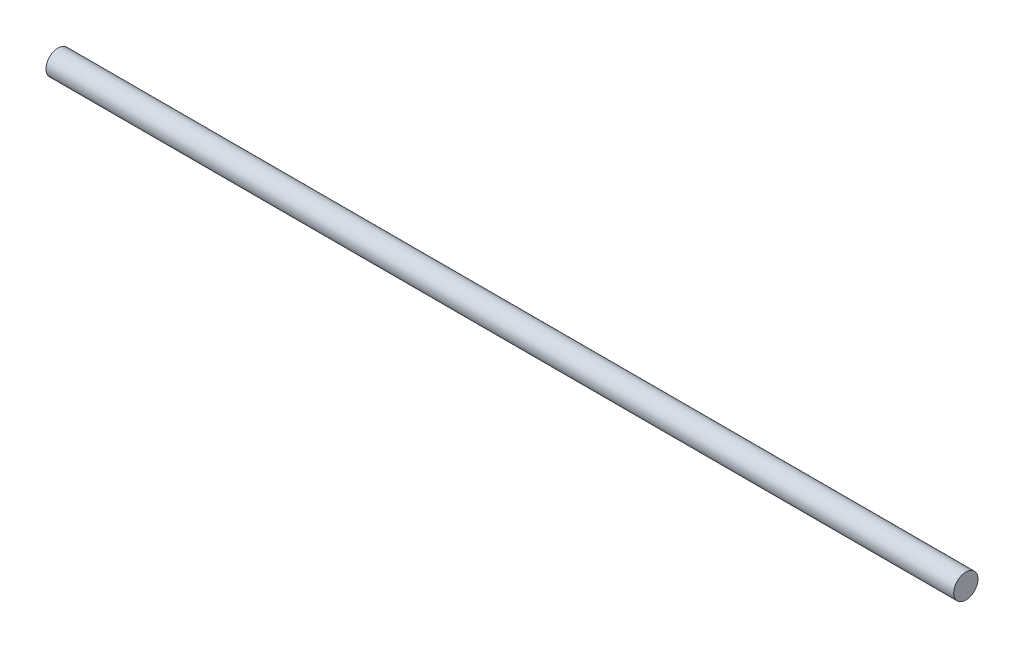
SolidWorks part; units mm, degrees
ref_plane "Front Plane" through (0, 0, 0) normal (0, 0, 1) x (1, 0, 0)
ref_plane "Top Plane" through (0, 0, 0) normal (0, 1, 0) x (1, 0, 0)
ref_plane "Right Plane" through (0, 0, 0) normal (1, 0, 0) x (0, 0, -1)
sketch "Sketch1" plane through (0, 0, 0) normal (1, 0, 0) x (0, 0, -1)
  circle A0 centre (0, 0) radius 4.7625
  dimension "D1" = 9.525
extrude "Boss-Extrude1" add sketch "Sketch1" along normal blind 355.6
